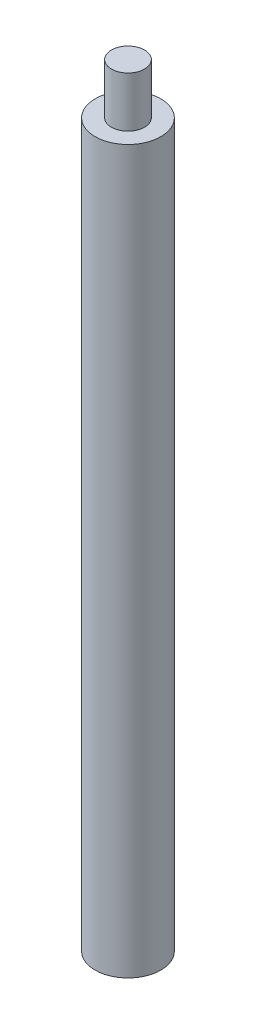
SolidWorks part; units mm, degrees
material "AISI 304"
ref_plane "Front" through (0, 0, 0) normal (0, 0, 1) x (1, 0, 0)
ref_plane "Top" through (0, 0, 0) normal (0, 1, 0) x (1, 0, 0)
ref_plane "Right" through (0, 0, 0) normal (1, 0, 0) x (0, 0, -1)
sketch "Sketch2" plane through (0, 0, 0) normal (0, 1, 0) x (1, 0, 0)
  circle A0 centre (0, 0) radius 1.9844
  dimension "D1" = 3.9688
extrude "Boss-Extrude1" add sketch "Sketch2" along normal blind 43.6372
sketch "Sketch3" plane through (0, 43.6372, 0) normal (0, 1, 0) x (1, 0, 0)
  circle A0 centre (0, 0) radius 1
  dimension "D1" = 2
extrude "Boss-Extrude2" add sketch "Sketch3" along normal blind 3.048
cosmetic thread "Cosmetic Thread1" parameters "D2"=1.548
sketch "Sketch4" plane through (0, 0, 0) normal (0, -1, 0) x (1, 0, 0)
  circle A0 centre (0, 0) radius 1
  dimension "D1" = 2
extrude "Cut-Extrude1" [suppressed] cut sketch "Sketch4" against normal blind 5
thread "Thread1" [suppressed] pitch 0.4 start angle 0, offset 0, length 0, pitch 0.4, diameter 2
ref_plane "Plane1" through (1, 0, 0) normal (0, 0, 1) x (1, 0, 0)
sketch "Thread Profile1" plane through (1, 0, 0) normal (0, 0, 1) x (1, 0, 0)
  line L0 (0, 0) -> (0, 0.4) construction
  line L1 (0, 0) -> (0.2165, 0.125)
  line L2 (0.2165, 0.125) -> (0.2165, 0.175)
  line L3 (0.2165, 0.175) -> (0, 0.3)
  line L4 (0.2165, 0.15) -> (0, 0.15) construction
  line L11 (0, 0) -> (0, 0.3)
  point P2 (0, 0)
  dimension "Pitch" = 0.4
  dimension "Profile_Angle" = 60
  dimension "Profile_Land" = 0.05
  dimension "Profile_Height" = 0.2165
thread "Thread2" [suppressed] pitch 0.4 start angle 0, offset 0, length 0, pitch 0.4, diameter 2
ref_plane "Plane2" through (-1, 46.382, 0) normal (0, 0, 1) x (-1, 0, 0)
sketch "Thread Profile2" plane through (-1, 46.382, 0) normal (0, 0, 1) x (-1, 0, 0)
  line L0 (0, 0) -> (0, 0.4) construction
  line L11 (0, 0) -> (0, 0.35)
  line L12 (0, 0.35) -> (-0.2165, 0.225)
  line L13 (-0.2165, 0.225) -> (-0.2165, 0.125)
  line L15 (-0.2165, 0.125) -> (0, 0)
  line L17 (-0.2165, 0.175) -> (0, 0.175) construction
  point P2 (0, 0)
  dimension "Pitch" = 0.4
  dimension "Profile_Angle" = 60
  dimension "Profile_Land" = 0.1
  dimension "Profile_Height" = 0.2165
hole_wizard "M2x0.4 Tapped Hole1" positions "Sketch5" profile "Sketch6" tap size "M2x0.4" standard "ANSI Metric"
sketch "Sketch5" plane through (0, 0, 0) normal (0, -1, 0) x (-1, 0, 0)
  point P0 (0, 0)
sketch "Sketch6" plane through (0, 0, 0) normal (1, 0, 0) x (0, 0, -1)
  line L0 (0, 0) -> (0, 5.6877)
  line L1 (0, 5.6877) -> (0.8, 5.207)
  line L2 (0.8, 5.207) -> (0.8, 0)
  line L5 (0.8, 0) -> (0, 0)
  line L10 (0, 5.6877) -> (-0.8, 5.207) construction
  line L11 (0, -6.35) -> (0, 107.95) construction
  dimension "Tap Drill Dia." = 1.6
  dimension "Tap Drill Depth" = 5.207
  dimension "Drill Angle" = 118
